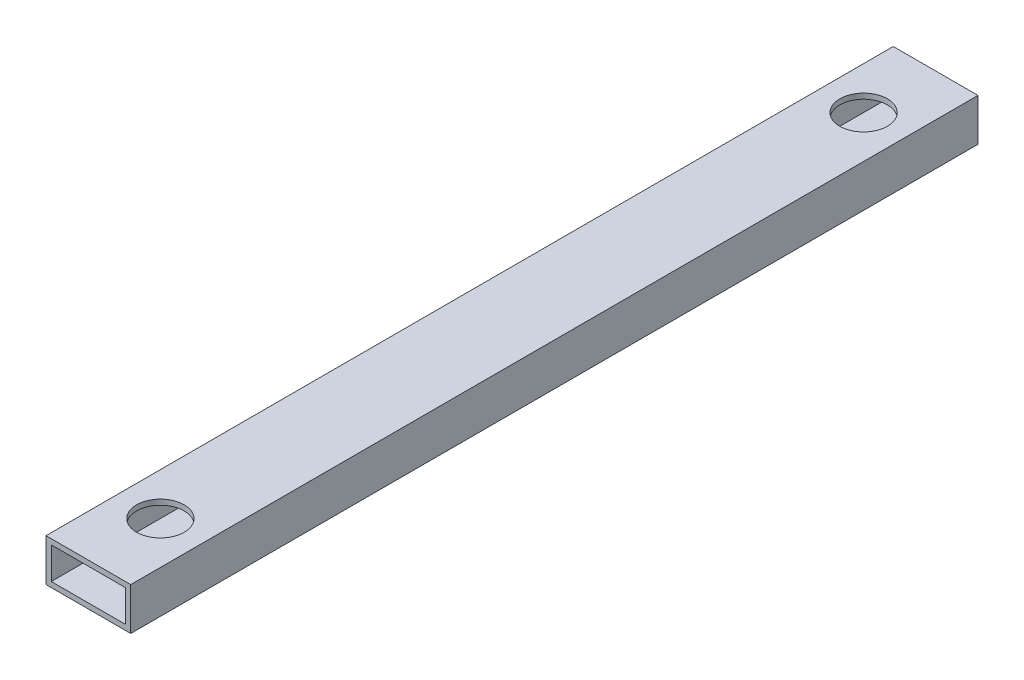
SolidWorks part; units mm, degrees
material "6061-T6 (SS)"
ref_plane "Front Plane" through (0, 0, 0) normal (0, 0, 1) x (1, 0, 0)
ref_plane "Top Plane" through (0, 0, 0) normal (0, 1, 0) x (1, 0, 0)
ref_plane "Right Plane" through (0, 0, 0) normal (1, 0, 0) x (0, 0, -1)
sketch "Sketch1" plane through (0, 0, 0) normal (0, 0, 1) x (1, 0, 0)
  line L0 (-25.4, 12.7) -> (25.4, -12.7) construction
  line L1 (-25.4, -12.7) -> (25.4, -12.7)
  line L2 (-25.4, -12.7) -> (-25.4, 12.7)
  line L3 (-25.4, 12.7) -> (25.4, 12.7)
  line L4 (25.4, -12.7) -> (25.4, 12.7)
  point P0 (0, 0)
  dimension "D1" = 25.4
  dimension "D2" = 50.8
extrude "Extrude-Thin1" add sketch "Sketch1" along normal blind 508 thin thin type one direction reverse wall 3.175
sketch "Sketch2" plane through (0, 12.7, 0) normal (0, 1, 0) x (1, 0, 0)
  line L0 (0, -508) -> (0, -464.82) construction
  line L2 (0, -464.82) -> (0, -43.18) construction
  line L3 (0, -43.18) -> (0, 0) construction
  line L5 (25.4, 0) -> (-25.4, 0) construction
  line L6 (25.4, -508) -> (-25.4, -508) construction
  circle A0 centre (0, -464.82) radius 14.2748
  circle A1 centre (0, -43.18) radius 14.2748
  point P2 (0, -508)
  point P8 (0, 0)
  dimension "D2" = 28.5496
  dimension "D1" = 421.64
extrude "Cut-Extrude1" cut sketch "Sketch2" against normal through all
